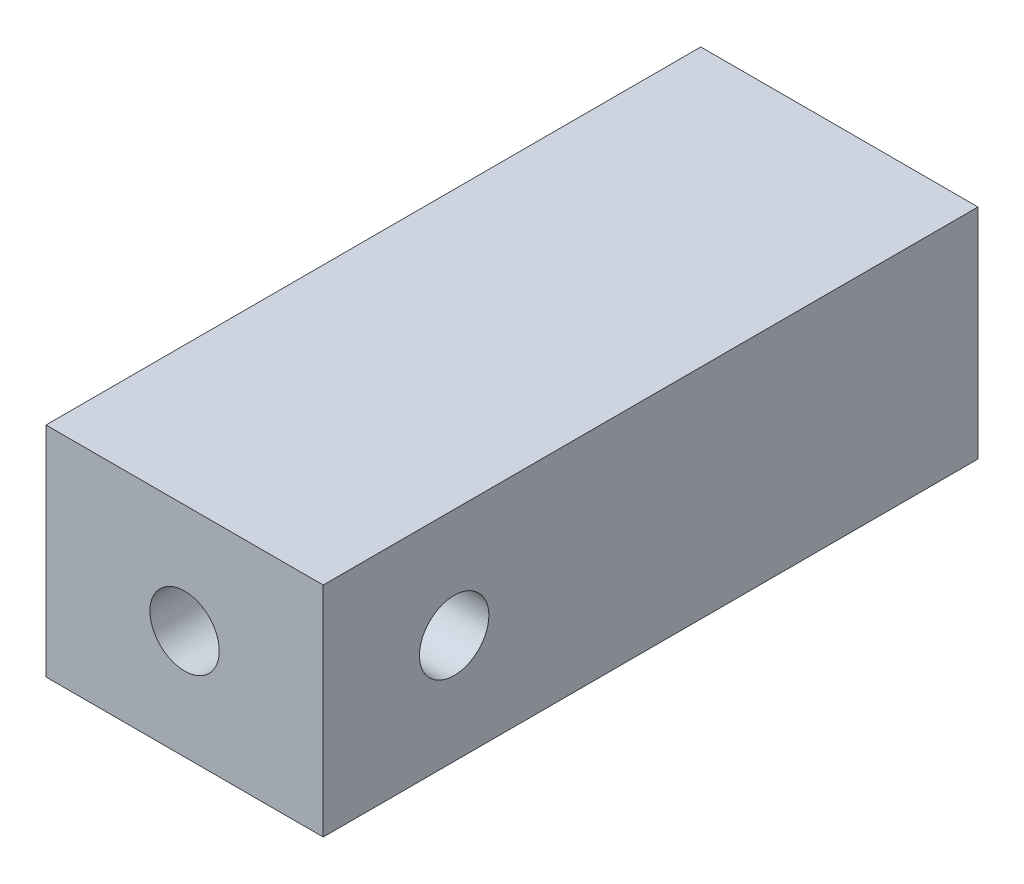
SolidWorks part; units mm, degrees
ref_plane "Front Plane" through (0, 0, 0) normal (0, 0, 1) x (1, 0, 0)
ref_plane "Top Plane" through (0, 0, 0) normal (0, 1, 0) x (1, 0, 0)
ref_plane "Right Plane" through (0, 0, 0) normal (1, 0, 0) x (0, 0, -1)
sketch "Sketch1" plane through (0, 0, 0) normal (0, 0, 1) x (1, 0, 0)
  line L1 (0, 0) -> (12.7, 0)
  line L2 (0, 0) -> (0, -10)
  line L3 (0, -10) -> (12.7, -10)
  line L4 (12.7, 0) -> (12.7, -10)
  circle A0 centre (6.35, -5) radius 1.5875
  point P7 (6.35, 0)
  point P8 (12.7, -5)
  dimension "D3" = 3.175
  dimension "D1" = 10
  dimension "D2" = 12.7
extrude "Boss-Extrude1" add sketch "Sketch1" along normal blind 30
sketch "Sketch2" plane through (0, 0, 0) normal (1, 0, 0) x (0, 0, -1)
  line L0 (-30, 0) -> (0, 0) construction
  line L1 (-30, -10) -> (-30, 0) construction
  circle A0 centre (-24, -5) radius 1.59
  dimension "D1" = 3.18
  dimension "D2" = 5
  dimension "D3" = 6
extrude "Cut-Extrude1" cut sketch "Sketch2" along normal blind 30
